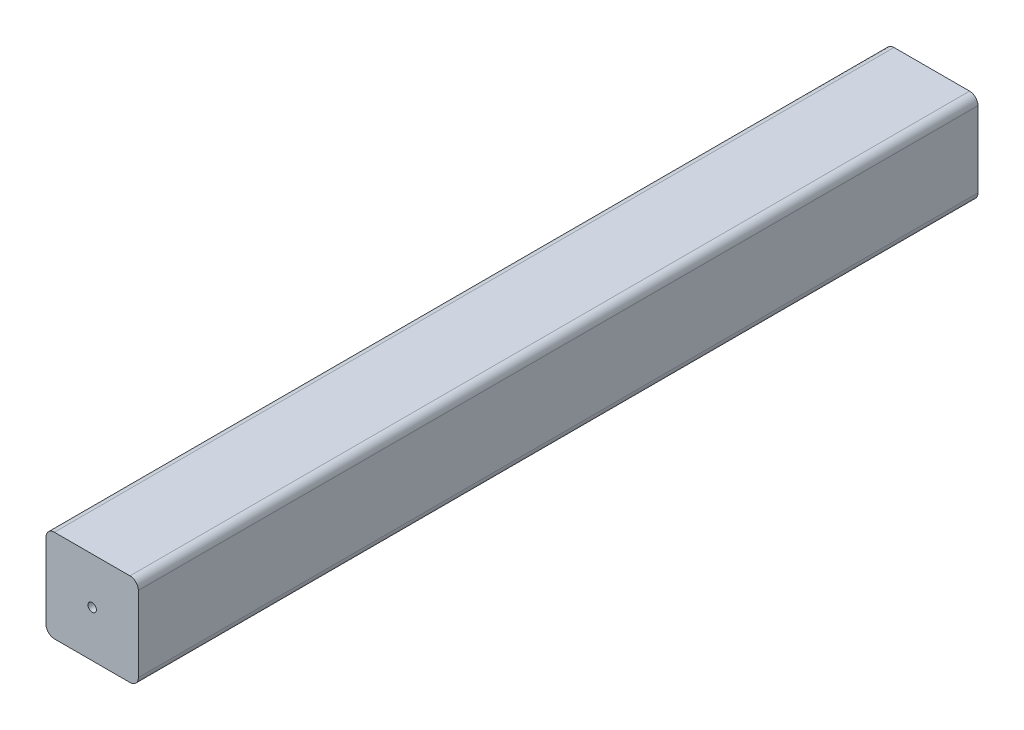
SolidWorks part; units mm, degrees
ref_plane "Plan de face" through (0, 0, 0) normal (0, 0, 1) x (1, 0, 0)
ref_plane "Plan de dessus" through (0, 0, 0) normal (0, 1, 0) x (1, 0, 0)
ref_plane "Plan de droite" through (0, 0, 0) normal (1, 0, 0) x (0, 0, -1)
sketch "Esquisse1" plane through (0, 0, 0) normal (0, 0, 1) x (1, 0, 0)
  line L1 (-9, 11) -> (9, 11)
  line L2 (11, 9) -> (11, -9)
  line L3 (9, -11) -> (-9, -11)
  line L4 (-11, -9) -> (-11, 9)
  arc A0 (-11, 9) -> (-9, 11) centre (-9, 9) cw
  arc A1 (9, 11) -> (11, 9) centre (9, 9) cw
  arc A2 (11, -9) -> (9, -11) centre (9, -9) cw
  arc A3 (-9, -11) -> (-11, -9) centre (-9, -9) cw
  circle A4 centre (0, 0) radius 1
  dimension "D1" = 2
extrude "Extrusion1" add sketch "Esquisse1" along normal blind 200
